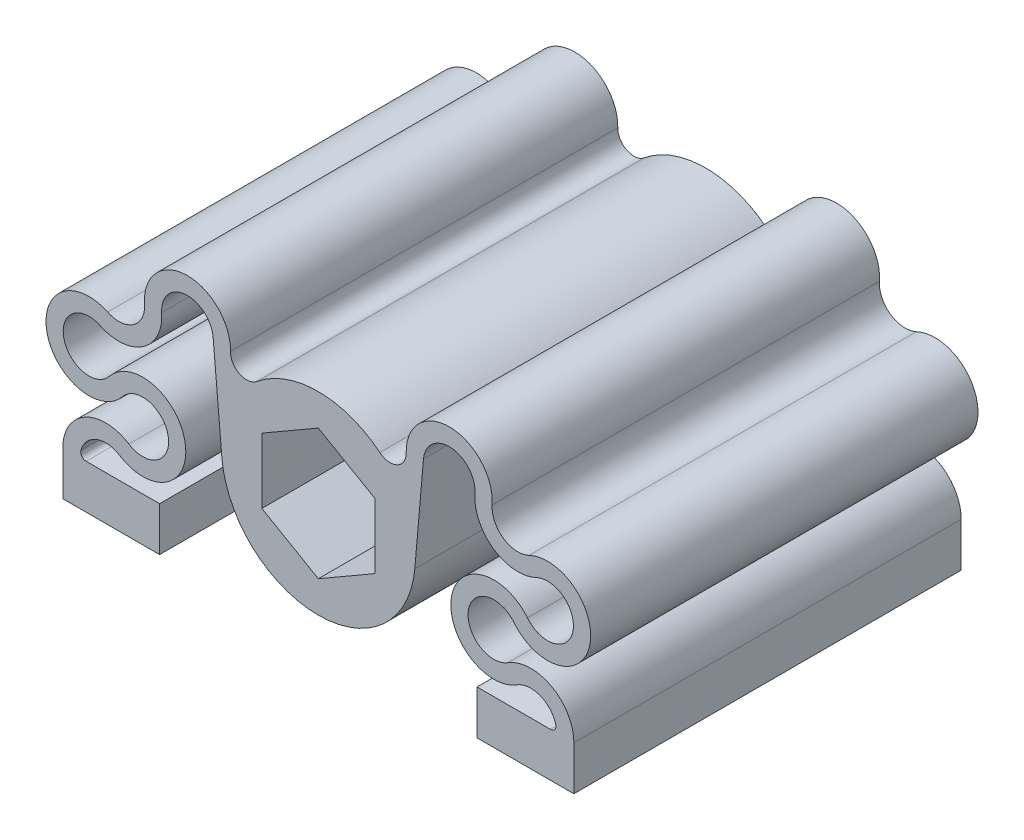
SolidWorks part; units mm, degrees
ref_plane "Front Plane" through (0, 0, 0) normal (0, 0, 1) x (1, 0, 0)
ref_plane "Top Plane" through (0, 0, 0) normal (0, 1, 0) x (1, 0, 0)
ref_plane "Right Plane" through (0, 0, 0) normal (1, 0, 0) x (0, 0, -1)
sketch "Sketch1" plane through (0, 0, 0) normal (0, 0, 1) x (1, 0, 0)
  line L0 (-14.75, -7.4) -> (-14.75, -11.5)
  line L1 (-21.583, -7.4) -> (-14.75, -7.4)
  line L2 (-23.75, -7.4) -> (-23.75, -11.5)
  line L3 (-23.75, -11.5) -> (-14.75, -11.5)
  line L4 (23.75, -7.4) -> (23.75, -11.5)
  line L5 (14.75, -7.4) -> (14.75, -11.5)
  line L6 (14.75, -11.5) -> (23.75, -11.5)
  line L7 (14.75, -7.4) -> (21.583, -7.4)
  line L8 (-14.75, -11.5) -> (14.75, -11.5) construction
  line L9 (0, -11.5) -> (0, 0) construction
  line L10 (-9.1862, 0) -> (0, 0) construction
  line L11 (2.8868, -5) -> (5.7735, 0) construction
  line L12 (5.7735, 0) -> (2.8868, 5) construction
  line L13 (2.8868, 5) -> (-2.8868, 5) construction
  line L14 (-2.8868, 5) -> (-5.7735, 0) construction
  line L15 (-5.7735, 0) -> (-2.8868, -5) construction
  line L16 (-2.8868, -5) -> (2.8868, -5) construction
  line L17 (-9.7745, 8.4592) -> (-8.9658, -0.7844)
  line L18 (9.7745, 8.4592) -> (8.9658, -0.7844)
  circle A0 centre (0, 0) radius 3.25
  arc A1 (-8.9658, -0.7844) -> (8.9658, -0.7844) centre (0, 0) ccw
  circle A2 centre (0, 0) radius 5 construction
  circle A3 centre (0, 0) radius 5.334 construction
  arc A4 (-20.2746, 4.1648) -> (-19.4374, 0.5) centre (-21.3109, 2) ccw
  arc A5 (-19.5838, 5.6079) -> (-18.1884, -0.5) centre (-21.3109, 2) ccw
  arc A6 (-17.6031, -4.025) -> (-18.1884, -0.5) centre (-16.3149, -2) ccw
  arc A7 (-18.4618, -5.375) -> (-19.4374, 0.5) centre (-16.3149, -2) ccw
  arc A8 (-17.6031, -4.025) -> (-23.75, -7.4) centre (-19.75, -7.4) ccw
  arc A9 (-18.4618, -5.375) -> (-22.0654, -6.7684) centre (-19.75, -7.4) ccw
  arc A10 (-19.5838, 5.6079) -> (-16.1542, 7.9517) centre (-18.5475, 7.7727) ccw
  arc A11 (-20.2746, 4.1648) -> (-14.5586, 8.071) centre (-18.5475, 7.7727) ccw
  arc A12 (-5.7146, 6.9529) -> (-8.1666, 8.1494) centre (-6.6671, 8.1117) cw
  arc A13 (18.4618, -5.375) -> (22.0654, -6.7684) centre (19.75, -7.4) cw
  arc A14 (17.6031, -4.025) -> (23.75, -7.4) centre (19.75, -7.4) cw
  arc A15 (17.6031, -4.025) -> (18.1884, -0.5) centre (16.3149, -2) cw
  arc A16 (18.4618, -5.375) -> (19.4374, 0.5) centre (16.3149, -2) cw
  arc A17 (9.7745, 8.4592) -> (14.5586, 8.071) centre (12.1653, 8.25) cw
  arc A18 (20.2746, 4.1648) -> (14.5586, 8.071) centre (18.5475, 7.7727) cw
  arc A19 (20.2746, 4.1648) -> (19.4374, 0.5) centre (21.3109, 2) cw
  arc A20 (19.5838, 5.6079) -> (18.1884, -0.5) centre (21.3109, 2) cw
  arc A21 (19.5838, 5.6079) -> (16.1542, 7.9517) centre (18.5475, 7.7727) cw
  arc A22 (5.7146, 6.9529) -> (-5.7146, 6.9529) centre (0, 0) ccw
  arc A23 (22.0654, -6.7684) -> (21.583, -7.4) centre (21.583, -6.9) cw
  arc A24 (-22.0654, -6.7684) -> (-21.583, -7.4) centre (-21.583, -6.9) ccw
  arc A25 (-8.1666, 8.1494) -> (-16.1542, 7.9517) centre (-12.1653, 8.25) ccw
  arc A26 (-9.7745, 8.4592) -> (-14.5586, 8.071) centre (-12.1653, 8.25) ccw
  arc A27 (8.1666, 8.1494) -> (16.1542, 7.9517) centre (12.1653, 8.25) cw
  arc A28 (5.7146, 6.9529) -> (8.1666, 8.1494) centre (6.6671, 8.1117) ccw
  point P55 (22.15, -7.4)
  point P58 (-22.15, -7.4)
  dimension "D5" = 6.5
  dimension "D6" = 18
  dimension "D7" = 10
  dimension "D8" = 5
  dimension "D9" = 1.6
  dimension "D10" = 8
  dimension "D11" = 1.5
  dimension "D15" = 0.5
  dimension "D14" = 19.75
  dimension "D1" = 11.5
  dimension "D2" = 47.5
  dimension "D3" = 9
  dimension "D4" = 4.1
  dimension "D12" = 9.5
  dimension "D13" = 13.5
extrude "Boss-Extrude1" add sketch "Sketch1" along normal blind 36
sketch "Sketch2" plane through (0, -11.5, 0) normal (0, -1, 0) x (1, 0, 0)
  line L0 (-19.225, 30.5) -> (19.225, 5.5) construction
  line L1 (0, 18) -> (23.75, 18) construction
  line L2 (23.75, 36) -> (23.75, 0) construction
  circle A0 centre (-19.225, 30.5) radius 2.6
  circle A1 centre (-19.225, 5.5) radius 2.6
  circle A2 centre (19.225, 5.5) radius 2.6
  circle A3 centre (19.225, 30.5) radius 2.6
  dimension "D3" = 5.2
  dimension "D1" = 38.45
  dimension "D2" = 25
extrude "Cut-Extrude1" cut sketch "Sketch2" against normal blind 4.2
sketch "Sketch5" plane through (0, 0, 0) normal (0, 0, 1) x (1, 0, 0)
  line L1 (5.25, -3.0311) -> (5.25, 3.0311)
  line L2 (5.25, 3.0311) -> (0, 6.0622)
  line L3 (0, 6.0622) -> (-5.25, 3.0311)
  line L4 (-5.25, 3.0311) -> (-5.25, -3.0311)
  line L5 (-5.25, -3.0311) -> (0, -6.0622)
  line L6 (0, -6.0622) -> (5.25, -3.0311)
  circle A0 centre (0, 0) radius 5.25 construction
  dimension "D1" = 10.5
extrude "Cut-Extrude3" cut sketch "Sketch5" along normal blind 7
sketch "Sketch3" plane through (0, 0, 36) normal (0, 0, 1) x (1, 0, 0)
  line L0 (5.25, -3.0311) -> (5.25, 3.0311) construction
  line L1 (5.25, 3.0311) -> (0, 6.0622) construction
  line L2 (0, -6.0622) -> (5.25, -3.0311) construction
  line L3 (-5.25, -3.0311) -> (0, -6.0622) construction
  line L6 (-5.25, 3.0311) -> (-5.25, -3.0311) construction
  line L7 (0, 6.0622) -> (-5.25, 3.0311) construction
  line L8 (5.25, -3.0311) -> (5.25, 3.0311)
  line L9 (5.25, 3.0311) -> (0, 6.0622)
  line L10 (0, -6.0622) -> (5.25, -3.0311)
  line L11 (-5.25, -3.0311) -> (0, -6.0622)
  line L12 (-5.25, 3.0311) -> (-5.25, -3.0311)
  line L13 (0, 6.0622) -> (-5.25, 3.0311)
extrude "Cut-Extrude2" cut sketch "Sketch3" against normal blind 24
sketch "Sketch6" plane through (0, 0, 7) normal (0, 0, -1) x (-1, 0, 0)
  circle A0 centre (0, 0) radius 3.25 construction
  circle A1 centre (0, 0) radius 3.25
extrude "Boss-Extrude2" add sketch "Sketch6" against normal blind 0.4
chamfer "Chamfer1" distance 1 angle 45 6 edges at (2.625, -4.5466, 0) (-2.625, -4.5466, 0) (-5.25, 0, 0) (-2.625, 4.5466, 0) (2.625, 4.5466, 0) (5.25, 0, 0)
